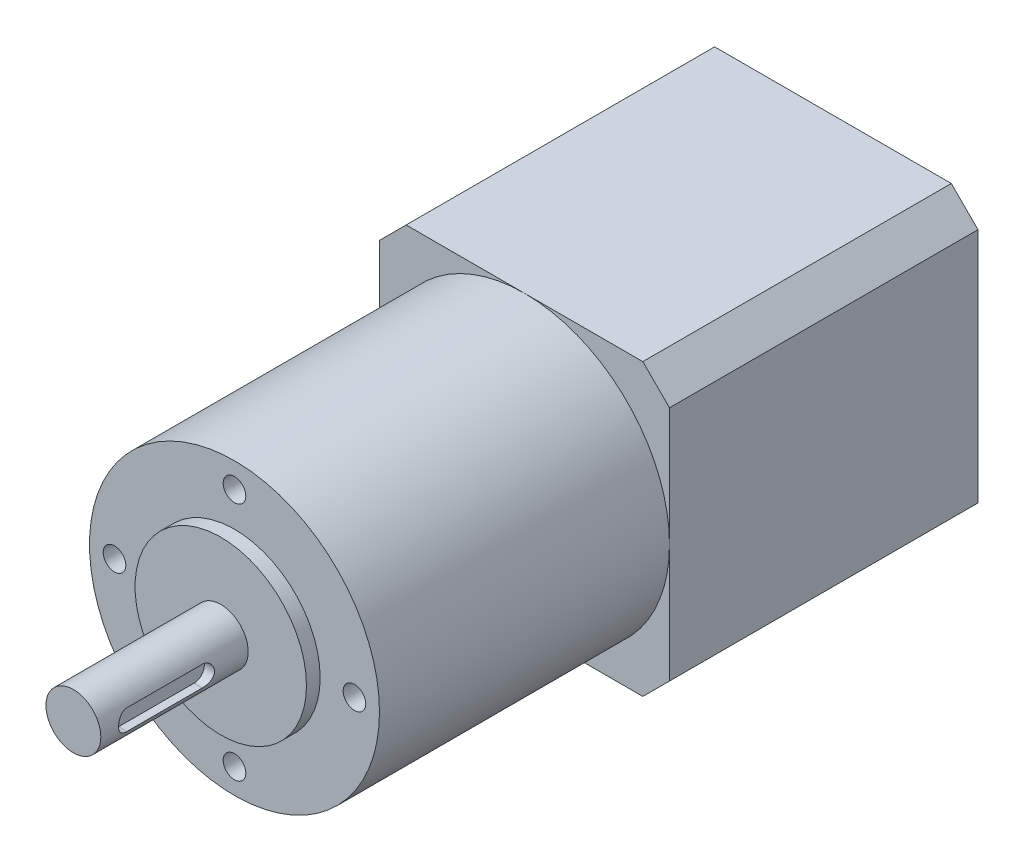
SolidWorks part; units mm, degrees
ref_plane "Front Plane" through (0, 0, 0) normal (0, 0, 1) x (1, 0, 0)
ref_plane "Top Plane" through (0, 0, 0) normal (0, 1, 0) x (1, 0, 0)
ref_plane "Right Plane" through (0, 0, 0) normal (1, 0, 0) x (0, 0, -1)
sketch "Sketch1" plane through (0, 0, 0) normal (0, 0, 1) x (1, 0, 0)
  line L0 (-21.15, 17.2609) -> (-17.2609, 21.15)
  line L1 (-17.2609, -21.15) -> (17.2609, -21.15)
  line L2 (-21.15, -17.2609) -> (-21.15, 17.2609)
  line L3 (-17.2609, 21.15) -> (17.2609, 21.15)
  line L4 (21.15, -17.2609) -> (21.15, 17.2609)
  line L5 (-21.15, -21.15) -> (21.15, 21.15) construction
  line L6 (-21.15, 21.15) -> (21.15, -21.15) construction
  line L7 (17.2609, 21.15) -> (21.15, 17.2609)
  line L8 (17.2609, -21.15) -> (21.15, -17.2609)
  line L9 (-21.15, -17.2609) -> (-17.2609, -21.15)
  point P0 (0, 0)
  point P14 (-13.4317, 21.5462)
  point P15 (-17.783, 22.8399)
  point P16 (0, 0)
  point P17 (0, 21.15)
  dimension "D1" = 42.3
  dimension "D2" = 5.5
  dimension "D3" = 135
extrude "Boss-Extrude1" add sketch "Sketch1" along normal blind 45
sketch "Sketch3" plane through (0, 0, 0) normal (1, 0, 0) x (0, 0, -1)
  line L0 (-45, 21.15) -> (-87.3, 21.15)
  line L1 (-87.3, 21.15) -> (-87.3, 12.5)
  line L2 (-87.3, 12.5) -> (-89.3, 12.5)
  line L3 (-89.3, 12.5) -> (-89.3, 4)
  line L4 (-89.3, 4) -> (-110.8, 4)
  line L5 (-110.8, 4) -> (-110.8, 0)
  line L6 (-110.8, 0) -> (-45, 0)
  line L7 (-45, -17.2609) -> (-45, 17.2609) construction
  line L8 (-45, 0) -> (-45, 21.15)
  point P7 (-90.5679, 11.8262)
  dimension "D1" = 42.3
  dimension "D2" = 12.5
  dimension "D3" = 2
  dimension "D4" = 4
  dimension "D5" = 23.5
revolve "Revolve1" add sketch "Sketch3" angle 360 about L6
sketch "Sketch4" plane through (0, 0, 87.3) normal (0, 0, 1) x (1, 0, 0)
  circle A0 centre (0, 17.5) radius 1.65
  circle A1 centre (17.5, 0) radius 1.65
  circle A2 centre (0, -17.5) radius 1.65
  circle A3 centre (-17.5, 0) radius 1.65
  point P2 (0, 15.977)
  point P3 (-2.9675, 15.924)
  point P4 (0, 0)
  point P11 (0, 0)
  dimension "D2" = 3.3
  dimension "D3" = 35
  dimension "D1" = 4
extrude "Cut-Extrude1" cut sketch "Sketch4" against normal blind 7
ref_plane "Plane1" through (4, 0, 0) normal (1, 0, 0) x (0, 0, -1)
sketch "Sketch5" plane through (4, 0, 0) normal (1, 0, 0) x (0, 0, -1)
  line L0 (-106.7, 0) -> (-95.7, 0) construction
  line L1 (-106.7, 1.5) -> (-95.7, 1.5)
  line L2 (-106.7, -1.5) -> (-95.7, -1.5)
  line L3 (-110.8, 4) -> (-110.8, -4) construction
  arc A0 (-106.7, 1.5) -> (-106.7, -1.5) centre (-106.7, 0) ccw
  arc A1 (-95.7, -1.5) -> (-95.7, 1.5) centre (-95.7, 0) ccw
  point P3 (-101.2, 0)
  point P8 (-108.2, 0)
  point P11 (-94.2, 0)
  dimension "D3" = 1.5
  dimension "D1" = 2.6
  dimension "D2" = 14
extrude "Cut-Extrude2" cut sketch "Sketch5" against normal blind 1.5
